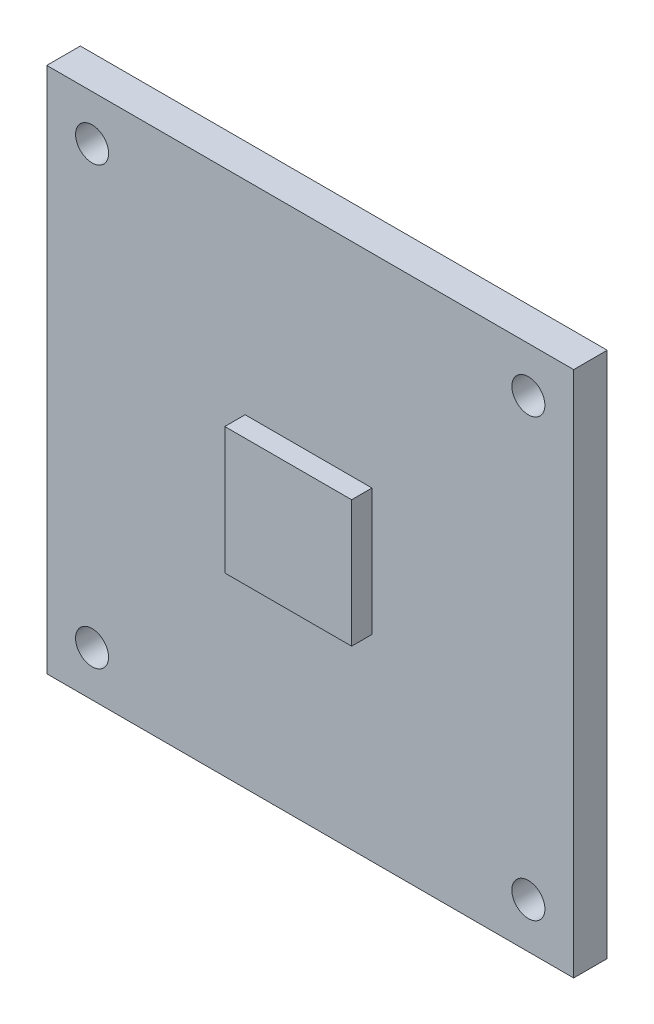
SolidWorks part; units mm, degrees
material "E-Fibra di vetro"
ref_plane "Piano frontale" through (0, 0, 0) normal (0, 0, 1) x (1, 0, 0)
ref_plane "Piano superiore" through (0, 0, 0) normal (0, 1, 0) x (1, 0, 0)
ref_plane "Piano destro" through (0, 0, 0) normal (1, 0, 0) x (0, 0, -1)
sketch "Model" plane through (0, 0, 0) normal (0, 0, 1) x (1, 0, 0)
  line L0 (11.583, 20.656) -> (11.983, 21.056)
  line L1 (11.983, 21.056) -> (20.783, 21.056)
  line L2 (20.783, 21.056) -> (21.183, 20.656)
  line L3 (21.183, 20.656) -> (21.183, 11.856)
  line L4 (21.183, 11.856) -> (20.783, 11.456)
  line L5 (20.783, 11.456) -> (11.983, 11.456)
  line L6 (11.983, 11.456) -> (11.583, 11.856)
  line L7 (11.583, 11.856) -> (11.583, 20.656)
  line L8 (8.395, 26.399) -> (8.395, 30.759)
  line L9 (8.395, 30.759) -> (8.395, 31.259)
  line L10 (13.195, 31.259) -> (13.195, 30.759)
  line L11 (13.195, 30.759) -> (13.195, 26.399)
  line L12 (8.395, 30.759) -> (13.195, 30.759)
  line L13 (25.1587, 28.956) -> (22.3393, 28.956)
  line L14 (22.3393, 28.956) -> (22.3393, 30.48)
  line L15 (22.3393, 30.48) -> (25.1587, 30.48)
  line L16 (25.1587, 30.48) -> (25.1587, 28.956)
  line L17 (25.376, 5.207) -> (25.376, 0.127)
  line L18 (25.376, 0.127) -> (22.376, 0.127)
  line L19 (22.376, 0.127) -> (22.376, 5.207)
  line L20 (22.376, 5.207) -> (25.376, 5.207)
  line L21 (-1.27, 8.255) -> (-1.27, 6.985)
  line L22 (-1.27, 6.985) -> (-1.905, 6.35)
  line L23 (-1.905, 6.35) -> (-3.175, 6.35)
  line L24 (-1.905, 11.43) -> (-1.27, 10.795)
  line L25 (-1.27, 10.795) -> (-1.27, 9.525)
  line L26 (-1.27, 9.525) -> (-1.905, 8.89)
  line L27 (-1.905, 8.89) -> (-3.175, 8.89)
  line L28 (-1.27, 8.255) -> (-1.905, 8.89)
  line L29 (-1.27, 15.875) -> (-1.27, 14.605)
  line L30 (-1.27, 14.605) -> (-1.905, 13.97)
  line L31 (-1.905, 13.97) -> (-3.175, 13.97)
  line L32 (-1.905, 13.97) -> (-1.27, 13.335)
  line L33 (-1.27, 13.335) -> (-1.27, 12.065)
  line L34 (-1.27, 12.065) -> (-1.905, 11.43)
  line L35 (-1.905, 11.43) -> (-3.175, 11.43)
  line L36 (-1.905, 16.51) -> (-3.175, 16.51)
  line L37 (-1.27, 15.875) -> (-1.905, 16.51)
  line L38 (-1.27, 5.715) -> (-1.27, 4.445)
  line L39 (-1.27, 4.445) -> (-1.905, 3.81)
  line L40 (-1.905, 3.81) -> (-3.175, 3.81)
  line L41 (-1.27, 5.715) -> (-1.905, 6.35)
  line L42 (-1.016, 27.559) -> (-1.016, 23.241)
  line L43 (-1.27, 27.813) -> (-2.794, 27.813)
  line L44 (-1.27, 22.987) -> (-2.794, 22.987)
  line L45 (-3.048, 23.241) -> (-3.048, 27.559)
  line L46 (25.4, -0.508) -> (26.67, -0.508)
  line L47 (26.67, -0.508) -> (27.305, -1.143)
  line L48 (27.305, -2.413) -> (26.67, -3.048)
  line L49 (27.305, -1.143) -> (27.94, -0.508)
  line L50 (27.94, -0.508) -> (29.21, -0.508)
  line L51 (29.21, -0.508) -> (29.845, -1.143)
  line L52 (29.845, -2.413) -> (29.21, -3.048)
  line L53 (29.21, -3.048) -> (27.94, -3.048)
  line L54 (27.94, -3.048) -> (27.305, -2.413)
  line L56 (25.4, -0.508) -> (24.765, -1.143)
  line L57 (24.765, -2.413) -> (25.4, -3.048)
  line L58 (26.67, -3.048) -> (25.4, -3.048)
  line L59 (29.845, -1.143) -> (29.845, -2.413)
  line L71 (7.3914, -2.9464) -> (8.6106, -2.9464)
  line L86 (27.889, 21.647) -> (24.689, 21.647)
  line L87 (27.889, 21.647) -> (27.889, 19.147)
  line L88 (27.889, 19.147) -> (24.689, 19.147)
  line L89 (24.689, 21.647) -> (24.689, 19.147)
  line L90 (36.449, -3.429) -> (-3.429, -3.429)
  line L91 (-3.429, -3.429) -> (-3.429, 36.449)
  line L92 (-3.429, 36.449) -> (36.449, 36.449)
  line L93 (36.449, 36.449) -> (36.449, -3.429)
  line L1654 (0, 2.921) -> (0, 2.667)
  line L1655 (0, -2.667) -> (0, -2.921)
  line L1658 (33.02, 35.941) -> (33.02, 35.687)
  line L1659 (33.02, 30.353) -> (33.02, 30.099)
  line L1660 (0, 35.941) -> (0, 35.687)
  line L1661 (0, 30.353) -> (0, 30.099)
  line L1662 (11.583, 20.656) -> (11.983, 21.056)
  line L1663 (11.983, 21.056) -> (20.783, 21.056)
  line L1664 (20.783, 21.056) -> (21.183, 20.656)
  line L1665 (21.183, 20.656) -> (21.183, 11.856)
  line L1666 (21.183, 11.856) -> (20.783, 11.456)
  line L1667 (20.783, 11.456) -> (11.983, 11.456)
  line L1668 (11.983, 11.456) -> (11.583, 11.856)
  line L1669 (11.583, 11.856) -> (11.583, 20.656)
  line L1670 (8.395, 26.399) -> (8.395, 30.759)
  line L1671 (8.395, 30.759) -> (8.395, 31.259)
  line L1672 (13.195, 31.259) -> (13.195, 30.759)
  line L1673 (13.195, 30.759) -> (13.195, 26.399)
  line L1674 (8.395, 30.759) -> (13.195, 30.759)
  line L1675 (25.1587, 28.956) -> (22.3393, 28.956)
  line L1676 (22.3393, 28.956) -> (22.3393, 30.48)
  line L1677 (22.3393, 30.48) -> (25.1587, 30.48)
  line L1678 (25.1587, 30.48) -> (25.1587, 28.956)
  line L1700 (25.376, 5.207) -> (25.376, 0.127)
  line L1701 (25.376, 0.127) -> (22.376, 0.127)
  line L1702 (22.376, 0.127) -> (22.376, 5.207)
  line L1703 (22.376, 5.207) -> (25.376, 5.207)
  line L1704 (-1.27, 8.255) -> (-1.27, 6.985)
  line L1705 (-1.27, 6.985) -> (-1.905, 6.35)
  line L1706 (-1.905, 6.35) -> (-3.175, 6.35)
  line L1707 (-3.175, 6.35) -> (-3.81, 6.985)
  line L1708 (-1.905, 11.43) -> (-1.27, 10.795)
  line L1709 (-1.27, 10.795) -> (-1.27, 9.525)
  line L1710 (-1.27, 9.525) -> (-1.905, 8.89)
  line L1711 (-1.905, 8.89) -> (-3.175, 8.89)
  line L1712 (-3.175, 8.89) -> (-3.81, 9.525)
  line L1713 (-3.81, 9.525) -> (-3.81, 10.795)
  line L1714 (-3.81, 10.795) -> (-3.175, 11.43)
  line L1715 (-1.27, 8.255) -> (-1.905, 8.89)
  line L1716 (-3.175, 8.89) -> (-3.81, 8.255)
  line L1717 (-3.81, 6.985) -> (-3.81, 8.255)
  line L1718 (-1.27, 15.875) -> (-1.27, 14.605)
  line L1719 (-1.27, 14.605) -> (-1.905, 13.97)
  line L1720 (-1.905, 13.97) -> (-3.175, 13.97)
  line L1721 (-3.175, 13.97) -> (-3.81, 14.605)
  line L1722 (-1.905, 13.97) -> (-1.27, 13.335)
  line L1723 (-1.27, 13.335) -> (-1.27, 12.065)
  line L1724 (-1.27, 12.065) -> (-1.905, 11.43)
  line L1725 (-1.905, 11.43) -> (-3.175, 11.43)
  line L1726 (-3.175, 11.43) -> (-3.81, 12.065)
  line L1727 (-3.81, 12.065) -> (-3.81, 13.335)
  line L1728 (-3.81, 13.335) -> (-3.175, 13.97)
  line L1729 (-1.905, 16.51) -> (-3.175, 16.51)
  line L1730 (-1.27, 15.875) -> (-1.905, 16.51)
  line L1731 (-3.175, 16.51) -> (-3.81, 15.875)
  line L1732 (-3.81, 14.605) -> (-3.81, 15.875)
  line L1733 (-1.27, 5.715) -> (-1.27, 4.445)
  line L1734 (-1.27, 4.445) -> (-1.905, 3.81)
  line L1735 (-1.905, 3.81) -> (-3.175, 3.81)
  line L1736 (-3.175, 3.81) -> (-3.81, 4.445)
  line L1737 (-1.27, 5.715) -> (-1.905, 6.35)
  line L1738 (-3.175, 6.35) -> (-3.81, 5.715)
  line L1739 (-3.81, 4.445) -> (-3.81, 5.715)
  line L1740 (-1.016, 27.559) -> (-1.016, 23.241)
  line L1741 (-1.27, 27.813) -> (-2.794, 27.813)
  line L1742 (-1.27, 22.987) -> (-2.794, 22.987)
  line L1743 (-3.048, 23.241) -> (-3.048, 27.559)
  line L1744 (25.4, -0.508) -> (26.67, -0.508)
  line L1745 (26.67, -0.508) -> (27.305, -1.143)
  line L1746 (27.305, -2.413) -> (26.67, -3.048)
  line L1747 (27.305, -1.143) -> (27.94, -0.508)
  line L1748 (27.94, -0.508) -> (29.21, -0.508)
  line L1749 (29.21, -0.508) -> (29.845, -1.143)
  line L1750 (29.845, -2.413) -> (29.21, -3.048)
  line L1751 (29.21, -3.048) -> (27.94, -3.048)
  line L1752 (27.94, -3.048) -> (27.305, -2.413)
  line L1754 (25.4, -0.508) -> (24.765, -1.143)
  line L1755 (24.765, -2.413) -> (25.4, -3.048)
  line L1756 (26.67, -3.048) -> (25.4, -3.048)
  line L1757 (29.845, -1.143) -> (29.845, -2.413)
  line L1773 (7.3914, -2.9464) -> (8.6106, -2.9464)
  line L1800 (27.889, 21.647) -> (24.689, 21.647)
  line L1801 (27.889, 21.647) -> (27.889, 19.147)
  line L1802 (27.889, 19.147) -> (24.689, 19.147)
  line L1803 (24.689, 21.647) -> (24.689, 19.147)
  arc A4 (12.0279, 21.0111) -> (11.9381, 21.1009) centre (11.983, 21.056) ccw
  arc A5 (11.5381, 20.7009) -> (11.6279, 20.6111) centre (11.583, 20.656) ccw
  arc A6 (20.783, 20.9925) -> (20.783, 21.1195) centre (20.783, 21.056) ccw
  arc A7 (11.983, 21.1195) -> (11.983, 20.9925) centre (11.983, 21.056) ccw
  arc A8 (21.1381, 20.6111) -> (21.2279, 20.7009) centre (21.183, 20.656) ccw
  arc A9 (20.8279, 21.1009) -> (20.7381, 21.0111) centre (20.783, 21.056) ccw
  arc A10 (21.1195, 11.856) -> (21.2465, 11.856) centre (21.183, 11.856) ccw
  arc A11 (21.2465, 20.656) -> (21.1195, 20.656) centre (21.183, 20.656) ccw
  arc A12 (20.7381, 11.5009) -> (20.8279, 11.4111) centre (20.783, 11.456) ccw
  arc A13 (21.2279, 11.8111) -> (21.1381, 11.9009) centre (21.183, 11.856) ccw
  arc A14 (11.983, 11.5195) -> (11.983, 11.3925) centre (11.983, 11.456) ccw
  arc A15 (20.783, 11.3925) -> (20.783, 11.5195) centre (20.783, 11.456) ccw
  arc A16 (11.6279, 11.9009) -> (11.5381, 11.8111) centre (11.583, 11.856) ccw
  arc A17 (11.9381, 11.4111) -> (12.0279, 11.5009) centre (11.983, 11.456) ccw
  arc A18 (11.6465, 20.656) -> (11.5195, 20.656) centre (11.583, 20.656) ccw
  arc A19 (11.5195, 11.856) -> (11.6465, 11.856) centre (11.583, 11.856) ccw
  arc A20 (8.4585, 30.759) -> (8.3315, 30.759) centre (8.395, 30.759) ccw
  arc A21 (8.3315, 26.399) -> (8.4585, 26.399) centre (8.395, 26.399) ccw
  arc A23 (8.3315, 30.759) -> (8.4585, 30.759) centre (8.395, 30.759) ccw
  arc A24 (13.1315, 30.759) -> (13.2585, 30.759) centre (13.195, 30.759) ccw
  arc A26 (13.1315, 26.399) -> (13.2585, 26.399) centre (13.195, 26.399) ccw
  arc A27 (13.2585, 30.759) -> (13.1315, 30.759) centre (13.195, 30.759) ccw
  arc A28 (13.195, 30.6955) -> (13.195, 30.8225) centre (13.195, 30.759) ccw
  arc A29 (8.395, 30.8225) -> (8.395, 30.6955) centre (8.395, 30.759) ccw
  arc A30 (22.3393, 29.0195) -> (22.3393, 28.8925) centre (22.3393, 28.956) ccw
  arc A31 (25.1587, 28.8925) -> (25.1587, 29.0195) centre (25.1587, 28.956) ccw
  arc A32 (22.4028, 30.48) -> (22.2758, 30.48) centre (22.3393, 30.48) ccw
  arc A33 (22.2758, 28.956) -> (22.4028, 28.956) centre (22.3393, 28.956) ccw
  arc A34 (25.1587, 30.4165) -> (25.1587, 30.5435) centre (25.1587, 30.48) ccw
  arc A35 (22.3393, 30.5435) -> (22.3393, 30.4165) centre (22.3393, 30.48) ccw
  arc A36 (25.0952, 28.956) -> (25.2222, 28.956) centre (25.1587, 28.956) ccw
  arc A37 (25.2222, 30.48) -> (25.0952, 30.48) centre (25.1587, 30.48) ccw
  arc A38 (25.3125, 0.127) -> (25.4395, 0.127) centre (25.376, 0.127) ccw
  arc A39 (25.4395, 5.207) -> (25.3125, 5.207) centre (25.376, 5.207) ccw
  arc A40 (22.376, 0.1905) -> (22.376, 0.0635) centre (22.376, 0.127) ccw
  arc A41 (25.376, 0.0635) -> (25.376, 0.1905) centre (25.376, 0.127) ccw
  arc A42 (22.4395, 5.207) -> (22.3125, 5.207) centre (22.376, 5.207) ccw
  arc A43 (22.3125, 0.127) -> (22.4395, 0.127) centre (22.376, 0.127) ccw
  arc A44 (25.376, 5.1435) -> (25.376, 5.2705) centre (25.376, 5.207) ccw
  arc A45 (22.376, 5.2705) -> (22.376, 5.1435) centre (22.376, 5.207) ccw
  arc A46 (-1.3335, 6.985) -> (-1.2065, 6.985) centre (-1.27, 6.985) ccw
  arc A47 (-1.2065, 8.255) -> (-1.3335, 8.255) centre (-1.27, 8.255) ccw
  arc A48 (-1.9499, 6.3949) -> (-1.8601, 6.3051) centre (-1.905, 6.35) ccw
  arc A49 (-1.2251, 6.9401) -> (-1.3149, 7.0299) centre (-1.27, 6.985) ccw
  arc A50 (-3.175, 6.4135) -> (-3.175, 6.2865) centre (-3.175, 6.35) ccw
  arc A51 (-1.905, 6.2865) -> (-1.905, 6.4135) centre (-1.905, 6.35) ccw
  arc A52 (-1.3149, 10.7501) -> (-1.2251, 10.8399) centre (-1.27, 10.795) ccw
  arc A53 (-1.8601, 11.4749) -> (-1.9499, 11.3851) centre (-1.905, 11.43) ccw
  arc A54 (-1.3335, 9.525) -> (-1.2065, 9.525) centre (-1.27, 9.525) ccw
  arc A55 (-1.2065, 10.795) -> (-1.3335, 10.795) centre (-1.27, 10.795) ccw
  arc A56 (-1.9499, 8.9349) -> (-1.8601, 8.8451) centre (-1.905, 8.89) ccw
  arc A57 (-1.2251, 9.4801) -> (-1.3149, 9.5699) centre (-1.27, 9.525) ccw
  arc A58 (-3.175, 8.9535) -> (-3.175, 8.8265) centre (-3.175, 8.89) ccw
  arc A59 (-1.905, 8.8265) -> (-1.905, 8.9535) centre (-1.905, 8.89) ccw
  arc A60 (-1.8601, 8.9349) -> (-1.9499, 8.8451) centre (-1.905, 8.89) ccw
  arc A61 (-1.3149, 8.2101) -> (-1.2251, 8.2999) centre (-1.27, 8.255) ccw
  arc A62 (-1.3335, 14.605) -> (-1.2065, 14.605) centre (-1.27, 14.605) ccw
  arc A63 (-1.2065, 15.875) -> (-1.3335, 15.875) centre (-1.27, 15.875) ccw
  arc A64 (-1.9499, 14.0149) -> (-1.8601, 13.9251) centre (-1.905, 13.97) ccw
  arc A65 (-1.2251, 14.5601) -> (-1.3149, 14.6499) centre (-1.27, 14.605) ccw
  arc A66 (-3.175, 14.0335) -> (-3.175, 13.9065) centre (-3.175, 13.97) ccw
  arc A67 (-1.905, 13.9065) -> (-1.905, 14.0335) centre (-1.905, 13.97) ccw
  arc A68 (-1.3149, 13.2901) -> (-1.2251, 13.3799) centre (-1.27, 13.335) ccw
  arc A69 (-1.8601, 14.0149) -> (-1.9499, 13.9251) centre (-1.905, 13.97) ccw
  arc A70 (-1.3335, 12.065) -> (-1.2065, 12.065) centre (-1.27, 12.065) ccw
  arc A71 (-1.2065, 13.335) -> (-1.3335, 13.335) centre (-1.27, 13.335) ccw
  arc A72 (-1.9499, 11.4749) -> (-1.8601, 11.3851) centre (-1.905, 11.43) ccw
  arc A73 (-1.2251, 12.0201) -> (-1.3149, 12.1099) centre (-1.27, 12.065) ccw
  arc A74 (-3.175, 11.4935) -> (-3.175, 11.3665) centre (-3.175, 11.43) ccw
  arc A75 (-1.905, 11.3665) -> (-1.905, 11.4935) centre (-1.905, 11.43) ccw
  arc A76 (-3.175, 16.5735) -> (-3.175, 16.4465) centre (-3.175, 16.51) ccw
  arc A77 (-1.905, 16.4465) -> (-1.905, 16.5735) centre (-1.905, 16.51) ccw
  arc A78 (-1.8601, 16.5549) -> (-1.9499, 16.4651) centre (-1.905, 16.51) ccw
  arc A79 (-1.3149, 15.8301) -> (-1.2251, 15.9199) centre (-1.27, 15.875) ccw
  arc A80 (-1.3335, 4.445) -> (-1.2065, 4.445) centre (-1.27, 4.445) ccw
  arc A81 (-1.2065, 5.715) -> (-1.3335, 5.715) centre (-1.27, 5.715) ccw
  arc A82 (-1.9499, 3.8549) -> (-1.8601, 3.7651) centre (-1.905, 3.81) ccw
  arc A83 (-1.2251, 4.4001) -> (-1.3149, 4.4899) centre (-1.27, 4.445) ccw
  arc A84 (-3.175, 3.8735) -> (-3.175, 3.7465) centre (-3.175, 3.81) ccw
  arc A85 (-1.905, 3.7465) -> (-1.905, 3.8735) centre (-1.905, 3.81) ccw
  arc A86 (-1.8601, 6.3949) -> (-1.9499, 6.3051) centre (-1.905, 6.35) ccw
  arc A87 (-1.3149, 5.6701) -> (-1.2251, 5.7599) centre (-1.27, 5.715) ccw
  arc A88 (-1.0795, 23.241) -> (-0.9525, 23.241) centre (-1.016, 23.241) ccw
  arc A89 (-0.9525, 27.559) -> (-1.0795, 27.559) centre (-1.016, 27.559) ccw
  arc A90 (-2.794, 27.813) -> (-3.048, 27.559) centre (-2.794, 27.559) ccw
  arc A91 (-2.794, 27.7495) -> (-2.794, 27.8765) centre (-2.794, 27.813) ccw
  arc A92 (-3.1115, 27.559) -> (-2.9845, 27.559) centre (-3.048, 27.559) ccw
  arc A93 (-3.048, 23.241) -> (-2.794, 22.987) centre (-2.794, 23.241) ccw
  arc A94 (-2.9845, 23.241) -> (-3.1115, 23.241) centre (-3.048, 23.241) ccw
  arc A95 (-2.794, 22.9235) -> (-2.794, 23.0505) centre (-2.794, 22.987) ccw
  arc A96 (-1.27, 22.987) -> (-1.016, 23.241) centre (-1.27, 23.241) ccw
  arc A97 (-1.27, 23.0505) -> (-1.27, 22.9235) centre (-1.27, 22.987) ccw
  arc A98 (-0.9525, 23.241) -> (-1.0795, 23.241) centre (-1.016, 23.241) ccw
  arc A99 (-1.016, 27.559) -> (-1.27, 27.813) centre (-1.27, 27.559) ccw
  arc A100 (-1.0795, 27.559) -> (-0.9525, 27.559) centre (-1.016, 27.559) ccw
  arc A101 (-1.27, 27.8765) -> (-1.27, 27.7495) centre (-1.27, 27.813) ccw
  arc A102 (-2.794, 27.8765) -> (-2.794, 27.7495) centre (-2.794, 27.813) ccw
  arc A103 (-1.27, 27.7495) -> (-1.27, 27.8765) centre (-1.27, 27.813) ccw
  arc A104 (-2.794, 23.0505) -> (-2.794, 22.9235) centre (-2.794, 22.987) ccw
  arc A105 (-1.27, 22.9235) -> (-1.27, 23.0505) centre (-1.27, 22.987) ccw
  arc A106 (-2.9845, 27.559) -> (-3.1115, 27.559) centre (-3.048, 27.559) ccw
  arc A107 (-3.1115, 23.241) -> (-2.9845, 23.241) centre (-3.048, 23.241) ccw
  arc A108 (26.67, -0.5715) -> (26.67, -0.4445) centre (26.67, -0.508) ccw
  arc A109 (25.4, -0.4445) -> (25.4, -0.5715) centre (25.4, -0.508) ccw
  arc A110 (27.2601, -1.1879) -> (27.3499, -1.0981) centre (27.305, -1.143) ccw
  arc A111 (26.7149, -0.4631) -> (26.6251, -0.5529) centre (26.67, -0.508) ccw
  arc A112 (26.6251, -3.0031) -> (26.7149, -3.0929) centre (26.67, -3.048) ccw
  arc A113 (27.3499, -2.4579) -> (27.2601, -2.3681) centre (27.305, -2.413) ccw
  arc A114 (27.9849, -0.5529) -> (27.8951, -0.4631) centre (27.94, -0.508) ccw
  arc A115 (27.2601, -1.0981) -> (27.3499, -1.1879) centre (27.305, -1.143) ccw
  arc A116 (29.21, -0.5715) -> (29.21, -0.4445) centre (29.21, -0.508) ccw
  arc A117 (27.94, -0.4445) -> (27.94, -0.5715) centre (27.94, -0.508) ccw
  arc A118 (29.8001, -1.1879) -> (29.8899, -1.0981) centre (29.845, -1.143) ccw
  arc A119 (29.2549, -0.4631) -> (29.1651, -0.5529) centre (29.21, -0.508) ccw
  arc A120 (29.1651, -3.0031) -> (29.2549, -3.0929) centre (29.21, -3.048) ccw
  arc A121 (29.8899, -2.4579) -> (29.8001, -2.3681) centre (29.845, -2.413) ccw
  arc A122 (27.94, -2.9845) -> (27.94, -3.1115) centre (27.94, -3.048) ccw
  arc A123 (29.21, -3.1115) -> (29.21, -2.9845) centre (29.21, -3.048) ccw
  arc A124 (27.3499, -2.3681) -> (27.2601, -2.4579) centre (27.305, -2.413) ccw
  arc A125 (27.8951, -3.0929) -> (27.9849, -3.0031) centre (27.94, -3.048) ccw
  arc A126 (24.7015, -2.413) -> (24.8285, -2.413) centre (24.765, -2.413) ccw
  arc A127 (24.8285, -1.143) -> (24.7015, -1.143) centre (24.765, -1.143) ccw
  arc A128 (24.7201, -1.0981) -> (24.8099, -1.1879) centre (24.765, -1.143) ccw
  arc A129 (25.4449, -0.5529) -> (25.3551, -0.4631) centre (25.4, -0.508) ccw
  arc A130 (25.3551, -3.0929) -> (25.4449, -3.0031) centre (25.4, -3.048) ccw
  arc A131 (24.8099, -2.3681) -> (24.7201, -2.4579) centre (24.765, -2.413) ccw
  arc A132 (25.4, -2.9845) -> (25.4, -3.1115) centre (25.4, -3.048) ccw
  arc A133 (26.67, -3.1115) -> (26.67, -2.9845) centre (26.67, -3.048) ccw
  arc A134 (29.7815, -2.413) -> (29.9085, -2.413) centre (29.845, -2.413) ccw
  arc A135 (29.9085, -1.143) -> (29.7815, -1.143) centre (29.845, -1.143) ccw
  arc A161 (8.6106, -3.0099) -> (8.6106, -2.8829) centre (8.6106, -2.9464) ccw
  arc A162 (7.3914, -2.8829) -> (7.3914, -3.0099) centre (7.3914, -2.9464) ccw
  arc A200 (24.689, 21.7105) -> (24.689, 21.5835) centre (24.689, 21.647) ccw
  arc A201 (27.889, 21.5835) -> (27.889, 21.7105) centre (27.889, 21.647) ccw
  arc A202 (27.8255, 19.147) -> (27.9525, 19.147) centre (27.889, 19.147) ccw
  arc A203 (27.9525, 21.647) -> (27.8255, 21.647) centre (27.889, 21.647) ccw
  arc A204 (24.689, 19.2105) -> (24.689, 19.0835) centre (24.689, 19.147) ccw
  arc A205 (27.889, 19.0835) -> (27.889, 19.2105) centre (27.889, 19.147) ccw
  arc A206 (24.6255, 19.147) -> (24.7525, 19.147) centre (24.689, 19.147) ccw
  arc A207 (24.7525, 21.647) -> (24.6255, 21.647) centre (24.689, 21.647) ccw
  arc A208 (-3.429, -3.4227) -> (-3.429, -3.4354) centre (-3.429, -3.429) ccw
  arc A209 (36.449, -3.4354) -> (36.449, -3.4227) centre (36.449, -3.429) ccw
  arc A210 (-3.4227, 36.449) -> (-3.4354, 36.449) centre (-3.429, 36.449) ccw
  arc A211 (-3.4354, -3.429) -> (-3.4227, -3.429) centre (-3.429, -3.429) ccw
  arc A212 (36.449, 36.4427) -> (36.449, 36.4554) centre (36.449, 36.449) ccw
  arc A213 (-3.429, 36.4554) -> (-3.429, 36.4427) centre (-3.429, 36.449) ccw
  arc A214 (36.4427, -3.429) -> (36.4554, -3.429) centre (36.449, -3.429) ccw
  arc A215 (36.4554, 36.449) -> (36.4427, 36.449) centre (36.449, 36.449) ccw
  circle A3336 centre (12.383, 20.256) radius 0.2827
  circle A3337 centre (22.676, 4.867) radius 0.25
  arc A3338 (-0.0127, 2.667) -> (0.0127, 2.667) centre (0, 2.667) ccw
  arc A3339 (0.0127, 2.921) -> (-0.0127, 2.921) centre (0, 2.921) ccw
  arc A3340 (-0.0127, -2.921) -> (0.0127, -2.921) centre (0, -2.921) ccw
  arc A3341 (0.0127, -2.667) -> (-0.0127, -2.667) centre (0, -2.667) ccw
  circle A3342 centre (0, 0) radius 2.921
  circle A3343 centre (0, 0) radius 1.5
  arc A3345 (33.0327, 2.921) -> (33.0073, 2.921) centre (33.02, 2.921) ccw
  arc A3346 (33.0073, -2.921) -> (33.0327, -2.921) centre (33.02, -2.921) ccw
  circle A3348 centre (33.02, 0) radius 2.921
  circle A3349 centre (33.02, 0) radius 1.5
  arc A3350 (33.0073, 35.687) -> (33.0327, 35.687) centre (33.02, 35.687) ccw
  arc A3351 (33.0327, 35.941) -> (33.0073, 35.941) centre (33.02, 35.941) ccw
  arc A3352 (33.0073, 30.099) -> (33.0327, 30.099) centre (33.02, 30.099) ccw
  arc A3353 (33.0327, 30.353) -> (33.0073, 30.353) centre (33.02, 30.353) ccw
  circle A3354 centre (33.02, 33.02) radius 2.921
  circle A3355 centre (33.02, 33.02) radius 1.5
  arc A3356 (-0.0127, 35.687) -> (0.0127, 35.687) centre (0, 35.687) ccw
  arc A3357 (0.0127, 35.941) -> (-0.0127, 35.941) centre (0, 35.941) ccw
  arc A3358 (-0.0127, 30.099) -> (0.0127, 30.099) centre (0, 30.099) ccw
  arc A3359 (0.0127, 30.353) -> (-0.0127, 30.353) centre (0, 30.353) ccw
  circle A3360 centre (0, 33.02) radius 2.921
  circle A3361 centre (0, 33.02) radius 1.5
  arc A3362 (12.0189, 21.0201) -> (11.9471, 21.0919) centre (11.983, 21.056) ccw
  arc A3363 (11.5471, 20.6919) -> (11.6189, 20.6201) centre (11.583, 20.656) ccw
  arc A3364 (20.783, 21.0052) -> (20.783, 21.1068) centre (20.783, 21.056) ccw
  arc A3365 (11.983, 21.1068) -> (11.983, 21.0052) centre (11.983, 21.056) ccw
  arc A3366 (21.1471, 20.6201) -> (21.2189, 20.6919) centre (21.183, 20.656) ccw
  arc A3367 (20.8189, 21.0919) -> (20.7471, 21.0201) centre (20.783, 21.056) ccw
  arc A3368 (21.1322, 11.856) -> (21.2338, 11.856) centre (21.183, 11.856) ccw
  arc A3369 (21.2338, 20.656) -> (21.1322, 20.656) centre (21.183, 20.656) ccw
  arc A3370 (20.7471, 11.4919) -> (20.8189, 11.4201) centre (20.783, 11.456) ccw
  arc A3371 (21.2189, 11.8201) -> (21.1471, 11.8919) centre (21.183, 11.856) ccw
  arc A3372 (11.983, 11.5068) -> (11.983, 11.4052) centre (11.983, 11.456) ccw
  arc A3373 (20.783, 11.4052) -> (20.783, 11.5068) centre (20.783, 11.456) ccw
  arc A3374 (11.6189, 11.8919) -> (11.5471, 11.8201) centre (11.583, 11.856) ccw
  arc A3375 (11.9471, 11.4201) -> (12.0189, 11.4919) centre (11.983, 11.456) ccw
  arc A3376 (11.6338, 20.656) -> (11.5322, 20.656) centre (11.583, 20.656) ccw
  arc A3377 (11.5322, 11.856) -> (11.6338, 11.856) centre (11.583, 11.856) ccw
  circle A3378 centre (12.383, 20.256) radius 0.2827
  arc A3379 (8.4458, 30.759) -> (8.3442, 30.759) centre (8.395, 30.759) ccw
  arc A3380 (8.3442, 26.399) -> (8.4458, 26.399) centre (8.395, 26.399) ccw
  arc A3382 (8.3442, 30.759) -> (8.4458, 30.759) centre (8.395, 30.759) ccw
  arc A3383 (13.1442, 30.759) -> (13.2458, 30.759) centre (13.195, 30.759) ccw
  arc A3385 (13.1442, 26.399) -> (13.2458, 26.399) centre (13.195, 26.399) ccw
  arc A3386 (13.2458, 30.759) -> (13.1442, 30.759) centre (13.195, 30.759) ccw
  arc A3387 (13.195, 30.7082) -> (13.195, 30.8098) centre (13.195, 30.759) ccw
  arc A3388 (8.395, 30.8098) -> (8.395, 30.7082) centre (8.395, 30.759) ccw
  arc A3389 (22.3393, 28.9878) -> (22.3393, 28.9243) centre (22.3393, 28.9561) ccw
  arc A3390 (25.1587, 28.9243) -> (25.1587, 28.9878) centre (25.1587, 28.9561) ccw
  arc A3391 (22.3711, 30.48) -> (22.3076, 30.48) centre (22.3393, 30.48) ccw
  arc A3392 (22.3076, 28.956) -> (22.3711, 28.956) centre (22.3393, 28.956) ccw
  arc A3393 (25.1587, 30.4483) -> (25.1587, 30.5117) centre (25.1587, 30.48) ccw
  arc A3394 (22.3393, 30.5117) -> (22.3393, 30.4483) centre (22.3393, 30.48) ccw
  arc A3395 (25.127, 28.956) -> (25.1904, 28.956) centre (25.1587, 28.956) ccw
  arc A3396 (25.1904, 30.48) -> (25.127, 30.48) centre (25.1587, 30.48) ccw
  arc A3439 (25.3443, 0.127) -> (25.4078, 0.127) centre (25.376, 0.127) ccw
  arc A3440 (25.4078, 5.207) -> (25.3443, 5.207) centre (25.376, 5.207) ccw
  arc A3441 (22.376, 0.1588) -> (22.376, 0.0953) centre (22.376, 0.127) ccw
  arc A3442 (25.376, 0.0953) -> (25.376, 0.1588) centre (25.376, 0.127) ccw
  arc A3443 (22.4078, 5.207) -> (22.3443, 5.207) centre (22.3761, 5.207) ccw
  arc A3444 (22.3443, 0.127) -> (22.4078, 0.127) centre (22.3761, 0.127) ccw
  arc A3445 (25.376, 5.1753) -> (25.376, 5.2387) centre (25.376, 5.207) ccw
  arc A3446 (22.376, 5.2387) -> (22.376, 5.1753) centre (22.376, 5.207) ccw
  circle A3447 centre (22.676, 4.867) radius 0.25
  arc A3448 (-1.3081, 6.985) -> (-1.2319, 6.985) centre (-1.27, 6.985) ccw
  arc A3449 (-1.2319, 8.255) -> (-1.3081, 8.255) centre (-1.27, 8.255) ccw
  arc A3450 (-1.9319, 6.3769) -> (-1.8781, 6.3231) centre (-1.905, 6.35) ccw
  arc A3451 (-1.2431, 6.9581) -> (-1.2969, 7.0119) centre (-1.27, 6.985) ccw
  arc A3452 (-3.175, 6.3881) -> (-3.175, 6.3119) centre (-3.175, 6.35) ccw
  arc A3453 (-1.905, 6.3119) -> (-1.905, 6.3881) centre (-1.905, 6.35) ccw
  arc A3454 (-3.7831, 7.0119) -> (-3.8369, 6.9581) centre (-3.81, 6.985) ccw
  arc A3455 (-3.2019, 6.3231) -> (-3.1481, 6.3769) centre (-3.175, 6.35) ccw
  arc A3456 (-1.2969, 10.7681) -> (-1.2431, 10.8219) centre (-1.27, 10.795) ccw
  arc A3457 (-1.8781, 11.4569) -> (-1.9319, 11.4031) centre (-1.905, 11.43) ccw
  arc A3458 (-1.3081, 9.525) -> (-1.2319, 9.525) centre (-1.27, 9.525) ccw
  arc A3459 (-1.2319, 10.795) -> (-1.3081, 10.795) centre (-1.27, 10.795) ccw
  arc A3460 (-1.9319, 8.9169) -> (-1.8781, 8.8631) centre (-1.905, 8.89) ccw
  arc A3461 (-1.2431, 9.4981) -> (-1.2969, 9.5519) centre (-1.27, 9.525) ccw
  arc A3462 (-3.175, 8.9281) -> (-3.175, 8.8519) centre (-3.175, 8.89) ccw
  arc A3463 (-1.905, 8.8519) -> (-1.905, 8.9281) centre (-1.905, 8.89) ccw
  arc A3464 (-3.7831, 9.5519) -> (-3.8369, 9.4981) centre (-3.81, 9.525) ccw
  arc A3465 (-3.2019, 8.8631) -> (-3.1481, 8.9169) centre (-3.175, 8.89) ccw
  arc A3466 (-3.7719, 10.795) -> (-3.8481, 10.795) centre (-3.81, 10.795) ccw
  arc A3467 (-3.8481, 9.525) -> (-3.7719, 9.525) centre (-3.81, 9.525) ccw
  arc A3468 (-3.1481, 11.4031) -> (-3.2019, 11.4569) centre (-3.175, 11.43) ccw
  arc A3469 (-3.8369, 10.8219) -> (-3.7831, 10.7681) centre (-3.81, 10.795) ccw
  arc A3470 (-1.8781, 8.9169) -> (-1.9319, 8.8631) centre (-1.905, 8.89) ccw
  arc A3471 (-1.2969, 8.2281) -> (-1.2431, 8.2819) centre (-1.27, 8.255) ccw
  arc A3472 (-3.8369, 8.2819) -> (-3.7831, 8.2281) centre (-3.81, 8.255) ccw
  arc A3473 (-3.1481, 8.8631) -> (-3.2019, 8.9169) centre (-3.175, 8.89) ccw
  arc A3474 (-3.7719, 8.255) -> (-3.8481, 8.255) centre (-3.81, 8.255) ccw
  arc A3475 (-3.8481, 6.985) -> (-3.7719, 6.985) centre (-3.81, 6.985) ccw
  arc A3476 (-1.3081, 14.605) -> (-1.2319, 14.605) centre (-1.27, 14.605) ccw
  arc A3477 (-1.2319, 15.875) -> (-1.3081, 15.875) centre (-1.27, 15.875) ccw
  arc A3478 (-1.9319, 13.9969) -> (-1.8781, 13.9431) centre (-1.905, 13.97) ccw
  arc A3479 (-1.2431, 14.5781) -> (-1.2969, 14.6319) centre (-1.27, 14.605) ccw
  arc A3480 (-3.175, 14.0081) -> (-3.175, 13.9319) centre (-3.175, 13.97) ccw
  arc A3481 (-1.905, 13.9319) -> (-1.905, 14.0081) centre (-1.905, 13.97) ccw
  arc A3482 (-3.7831, 14.6319) -> (-3.8369, 14.5781) centre (-3.81, 14.605) ccw
  arc A3483 (-3.2019, 13.9431) -> (-3.1481, 13.9969) centre (-3.175, 13.97) ccw
  arc A3484 (-1.2969, 13.3081) -> (-1.2431, 13.3619) centre (-1.27, 13.335) ccw
  arc A3485 (-1.8781, 13.9969) -> (-1.9319, 13.9431) centre (-1.905, 13.97) ccw
  arc A3486 (-1.3081, 12.065) -> (-1.2319, 12.065) centre (-1.27, 12.065) ccw
  arc A3487 (-1.2319, 13.335) -> (-1.3081, 13.335) centre (-1.27, 13.335) ccw
  arc A3488 (-1.9319, 11.4569) -> (-1.8781, 11.4031) centre (-1.905, 11.43) ccw
  arc A3489 (-1.2431, 12.0381) -> (-1.2969, 12.0919) centre (-1.27, 12.065) ccw
  arc A3490 (-3.175, 11.4681) -> (-3.175, 11.3919) centre (-3.175, 11.43) ccw
  arc A3491 (-1.905, 11.3919) -> (-1.905, 11.4681) centre (-1.905, 11.43) ccw
  arc A3492 (-3.7831, 12.0919) -> (-3.8369, 12.0381) centre (-3.81, 12.065) ccw
  arc A3493 (-3.2019, 11.4031) -> (-3.1481, 11.4569) centre (-3.175, 11.43) ccw
  arc A3494 (-3.7719, 13.335) -> (-3.8481, 13.335) centre (-3.81, 13.335) ccw
  arc A3495 (-3.8481, 12.065) -> (-3.7719, 12.065) centre (-3.81, 12.065) ccw
  arc A3496 (-3.1481, 13.9431) -> (-3.2019, 13.9969) centre (-3.175, 13.97) ccw
  arc A3497 (-3.8369, 13.3619) -> (-3.7831, 13.3081) centre (-3.81, 13.335) ccw
  arc A3498 (-3.175, 16.5481) -> (-3.175, 16.4719) centre (-3.175, 16.51) ccw
  arc A3499 (-1.905, 16.4719) -> (-1.905, 16.5481) centre (-1.905, 16.51) ccw
  arc A3500 (-1.8781, 16.5369) -> (-1.9319, 16.4831) centre (-1.905, 16.51) ccw
  arc A3501 (-1.2969, 15.8481) -> (-1.2431, 15.9019) centre (-1.27, 15.875) ccw
  arc A3502 (-3.8369, 15.9019) -> (-3.7831, 15.8481) centre (-3.81, 15.875) ccw
  arc A3503 (-3.1481, 16.4831) -> (-3.2019, 16.5369) centre (-3.175, 16.51) ccw
  arc A3504 (-3.7719, 15.875) -> (-3.8481, 15.875) centre (-3.81, 15.875) ccw
  arc A3505 (-3.8481, 14.605) -> (-3.7719, 14.605) centre (-3.81, 14.605) ccw
  arc A3506 (-1.3081, 4.445) -> (-1.2319, 4.445) centre (-1.27, 4.445) ccw
  arc A3507 (-1.2319, 5.715) -> (-1.3081, 5.715) centre (-1.27, 5.715) ccw
  arc A3508 (-1.9319, 3.8369) -> (-1.8781, 3.7831) centre (-1.905, 3.81) ccw
  arc A3509 (-1.2431, 4.4181) -> (-1.2969, 4.4719) centre (-1.27, 4.445) ccw
  arc A3510 (-3.175, 3.8481) -> (-3.175, 3.7719) centre (-3.175, 3.81) ccw
  arc A3511 (-1.905, 3.7719) -> (-1.905, 3.8481) centre (-1.905, 3.81) ccw
  arc A3512 (-3.7831, 4.4719) -> (-3.8369, 4.4181) centre (-3.81, 4.445) ccw
  arc A3513 (-3.2019, 3.7831) -> (-3.1481, 3.8369) centre (-3.175, 3.81) ccw
  arc A3514 (-1.8781, 6.3769) -> (-1.9319, 6.3231) centre (-1.905, 6.35) ccw
  arc A3515 (-1.2969, 5.6881) -> (-1.2431, 5.7419) centre (-1.27, 5.715) ccw
  arc A3516 (-3.8369, 5.7419) -> (-3.7831, 5.6881) centre (-3.81, 5.715) ccw
  arc A3517 (-3.1481, 6.3231) -> (-3.2019, 6.3769) centre (-3.175, 6.35) ccw
  arc A3518 (-3.7719, 5.715) -> (-3.8481, 5.715) centre (-3.81, 5.715) ccw
  arc A3519 (-3.8481, 4.445) -> (-3.7719, 4.445) centre (-3.81, 4.445) ccw
  arc A3520 (-1.0541, 23.241) -> (-0.9779, 23.241) centre (-1.016, 23.241) ccw
  arc A3521 (-0.9779, 27.559) -> (-1.0541, 27.559) centre (-1.016, 27.559) ccw
  arc A3522 (-2.794, 27.813) -> (-3.048, 27.559) centre (-2.794, 27.559) ccw
  arc A3523 (-2.794, 27.7749) -> (-2.794, 27.8511) centre (-2.794, 27.813) ccw
  arc A3524 (-3.0861, 27.559) -> (-3.0099, 27.559) centre (-3.048, 27.559) ccw
  arc A3525 (-3.048, 23.241) -> (-2.794, 22.987) centre (-2.794, 23.241) ccw
  arc A3526 (-3.0099, 23.241) -> (-3.0861, 23.241) centre (-3.048, 23.241) ccw
  arc A3527 (-2.794, 22.9489) -> (-2.794, 23.0251) centre (-2.794, 22.987) ccw
  arc A3528 (-1.27, 22.987) -> (-1.016, 23.241) centre (-1.27, 23.241) ccw
  arc A3529 (-1.27, 23.0251) -> (-1.27, 22.9489) centre (-1.27, 22.987) ccw
  arc A3530 (-0.9779, 23.241) -> (-1.0541, 23.241) centre (-1.016, 23.241) ccw
  arc A3531 (-1.016, 27.559) -> (-1.27, 27.813) centre (-1.27, 27.559) ccw
  arc A3532 (-1.0541, 27.559) -> (-0.9779, 27.559) centre (-1.016, 27.559) ccw
  arc A3533 (-1.27, 27.8511) -> (-1.27, 27.7749) centre (-1.27, 27.813) ccw
  arc A3534 (-2.794, 27.8511) -> (-2.794, 27.7749) centre (-2.794, 27.813) ccw
  arc A3535 (-1.27, 27.7749) -> (-1.27, 27.8511) centre (-1.27, 27.813) ccw
  arc A3536 (-2.794, 23.0251) -> (-2.794, 22.9489) centre (-2.794, 22.987) ccw
  arc A3537 (-1.27, 22.9489) -> (-1.27, 23.0251) centre (-1.27, 22.987) ccw
  arc A3538 (-3.0099, 27.559) -> (-3.0861, 27.559) centre (-3.048, 27.559) ccw
  arc A3539 (-3.0861, 23.241) -> (-3.0099, 23.241) centre (-3.048, 23.241) ccw
  arc A3540 (26.67, -0.5588) -> (26.67, -0.4572) centre (26.67, -0.508) ccw
  arc A3541 (25.4, -0.4572) -> (25.4, -0.5588) centre (25.4, -0.508) ccw
  arc A3542 (27.2691, -1.1789) -> (27.3409, -1.1071) centre (27.305, -1.143) ccw
  arc A3543 (26.7059, -0.4721) -> (26.6341, -0.5439) centre (26.67, -0.508) ccw
  arc A3544 (26.6341, -3.0121) -> (26.7059, -3.0839) centre (26.67, -3.048) ccw
  arc A3545 (27.3409, -2.4489) -> (27.2691, -2.3771) centre (27.305, -2.413) ccw
  arc A3546 (27.9759, -0.5439) -> (27.9041, -0.4721) centre (27.94, -0.508) ccw
  arc A3547 (27.2691, -1.1071) -> (27.3409, -1.1789) centre (27.305, -1.143) ccw
  arc A3548 (29.21, -0.5588) -> (29.21, -0.4572) centre (29.21, -0.508) ccw
  arc A3549 (27.94, -0.4572) -> (27.94, -0.5588) centre (27.94, -0.508) ccw
  arc A3550 (29.8091, -1.1789) -> (29.8809, -1.1071) centre (29.845, -1.143) ccw
  arc A3551 (29.2459, -0.4721) -> (29.1741, -0.5439) centre (29.21, -0.508) ccw
  arc A3552 (29.1741, -3.0121) -> (29.2459, -3.0839) centre (29.21, -3.048) ccw
  arc A3553 (29.8809, -2.4489) -> (29.8091, -2.3771) centre (29.845, -2.413) ccw
  arc A3554 (27.94, -2.9972) -> (27.94, -3.0988) centre (27.94, -3.048) ccw
  arc A3555 (29.21, -3.0988) -> (29.21, -2.9972) centre (29.21, -3.048) ccw
  arc A3556 (27.3409, -2.3771) -> (27.2691, -2.4489) centre (27.305, -2.413) ccw
  arc A3557 (27.9041, -3.0839) -> (27.9759, -3.0121) centre (27.94, -3.048) ccw
  arc A3558 (24.7142, -2.413) -> (24.8158, -2.413) centre (24.765, -2.413) ccw
  arc A3559 (24.8158, -1.143) -> (24.7142, -1.143) centre (24.765, -1.143) ccw
  arc A3560 (24.7291, -1.1071) -> (24.8009, -1.1789) centre (24.765, -1.143) ccw
  arc A3561 (25.4359, -0.5439) -> (25.3641, -0.4721) centre (25.4, -0.508) ccw
  arc A3562 (25.3641, -3.0839) -> (25.4359, -3.0121) centre (25.4, -3.048) ccw
  arc A3563 (24.8009, -2.3771) -> (24.7291, -2.4489) centre (24.765, -2.413) ccw
  arc A3564 (25.4, -2.9972) -> (25.4, -3.0988) centre (25.4, -3.048) ccw
  arc A3565 (26.67, -3.0988) -> (26.67, -2.9972) centre (26.67, -3.048) ccw
  arc A3566 (29.7942, -2.413) -> (29.8958, -2.413) centre (29.845, -2.413) ccw
  arc A3567 (29.8958, -1.143) -> (29.7942, -1.143) centre (29.845, -1.143) ccw
  arc A3598 (8.6106, -2.9845) -> (8.6106, -2.9083) centre (8.6106, -2.9464) ccw
  arc A3599 (7.3914, -2.9083) -> (7.3914, -2.9845) centre (7.3914, -2.9464) ccw
  arc A3652 (24.689, 21.6788) -> (24.689, 21.6153) centre (24.689, 21.6471) ccw
  arc A3653 (27.889, 21.6153) -> (27.889, 21.6788) centre (27.889, 21.6471) ccw
  arc A3654 (27.8573, 19.147) -> (27.9208, 19.147) centre (27.889, 19.147) ccw
  arc A3655 (27.9208, 21.647) -> (27.8573, 21.647) centre (27.889, 21.647) ccw
  arc A3656 (24.689, 19.1788) -> (24.689, 19.1153) centre (24.689, 19.1471) ccw
  arc A3657 (27.889, 19.1153) -> (27.889, 19.1788) centre (27.889, 19.1471) ccw
  arc A3658 (24.6573, 19.147) -> (24.7207, 19.147) centre (24.689, 19.147) ccw
  arc A3659 (24.7207, 21.647) -> (24.6573, 21.647) centre (24.689, 21.647) ccw
  dimension "D1" = 39.878
  dimension "D2" = 33.02
sketch "Schizzo2" plane through (0, 0, 0) normal (0, 0, 1) x (1, 0, 0)
  line L1 (-3.429, 36.449) -> (36.449, 36.449)
  line L2 (-3.429, 36.449) -> (-3.429, -3.429)
  line L3 (-3.429, -3.429) -> (36.449, -3.429)
  line L4 (36.449, 36.449) -> (36.449, -3.429)
extrude "Estrusione-Estrusione1" add sketch "Schizzo2" against normal blind 2.54
hole_wizard "Foro filettato M3x0.5-1" positions "Schizzo4" profile "Schizzo3" tap size "M3x0.5" standard "Ansi Metric" end condition through all
sketch "Schizzo4" plane through (0, 0, 0) normal (0, 0, 1) x (1, 0, 0)
  point P0 (0, 33.02)
  point P3 (33.02, 33.02)
  point P6 (33.02, 0)
  point P9 (0, 0)
sketch "Schizzo3" plane through (0, 33.02, 0) normal (1, 0, 0) x (0, -1, 0)
  line L0 (0, 0) -> (0, 2.54)
  line L1 (0, 2.54) -> (1.25, 2.54)
  line L2 (1.25, 2.54) -> (1.25, 0)
  line L5 (1.25, 0) -> (0, 0)
  line L11 (0, -6.35) -> (0, 107.95) construction
  dimension "Thru Tap Drill Dia." = 2.5
  dimension "Thru Tap Drill Depth" = 2.54
cosmetic thread "Filettatura del foro1" parameters "D2"=3
cosmetic thread "Filettatura del foro2" parameters "D2"=3
cosmetic thread "Filettatura del foro3" parameters "D2"=3
cosmetic thread "Filettatura del foro4" parameters "D2"=3
sketch "Schizzo5" plane through (0, 0, 0) normal (0, 0, 1) x (1, 0, 0)
  line L0 (11.583, 11.856) -> (11.583, 20.656) construction
  line L1 (11.583, 11.456) -> (21.183, 11.456)
  line L2 (11.583, 11.456) -> (11.583, 21.056)
  line L3 (11.583, 21.056) -> (21.183, 21.056)
  line L4 (21.183, 11.456) -> (21.183, 21.056)
  line L5 (11.983, 21.056) -> (20.783, 21.056) construction
  line L6 (20.783, 11.456) -> (11.983, 11.456) construction
  line L7 (21.183, 20.656) -> (21.183, 11.856) construction
extrude "Estrusione-Estrusione2" add sketch "Schizzo5" along normal blind 1.54
